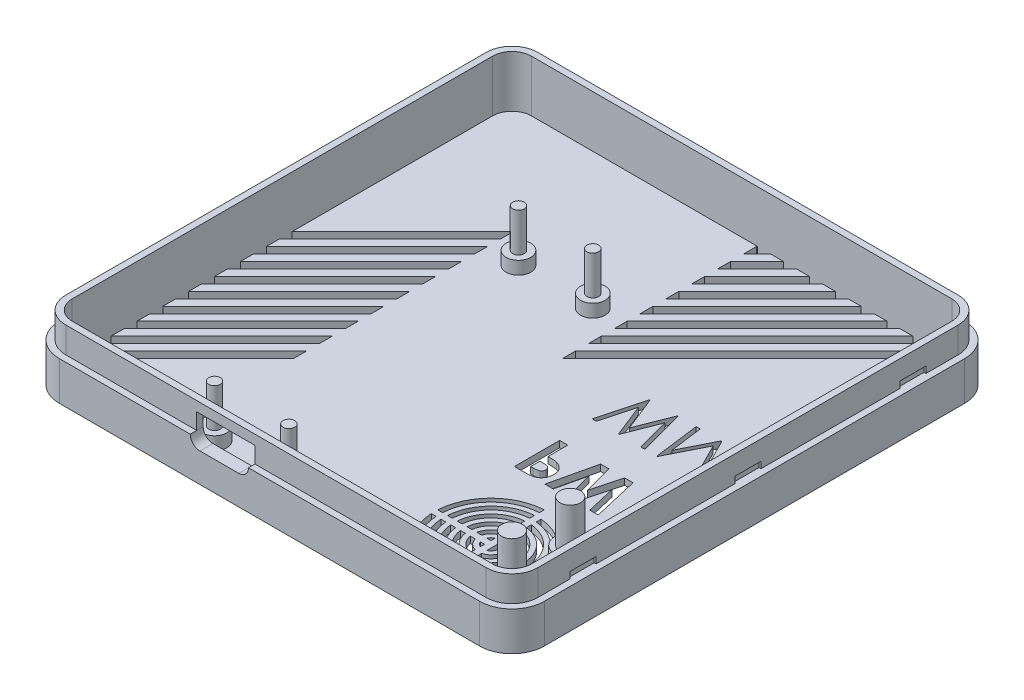
SolidWorks part; units mm, degrees
material "ABS"
ref_plane "Płaszczyzna przednia" through (0, 0, 0) normal (0, 0, 1) x (1, 0, 0)
ref_plane "Płaszczyzna górna" through (0, 0, 0) normal (0, 1, 0) x (1, 0, 0)
ref_plane "Płaszczyzna prawa" through (0, 0, 0) normal (1, 0, 0) x (0, 0, -1)
sketch "Szkic1" plane through (0, 0, 0) normal (0, 1, 0) x (1, 0, 0)
  line L0 (0, 0) -> (0, 75)
  line L1 (0, 75) -> (75, 75)
  line L2 (75, 75) -> (75, 0)
  line L3 (75, 0) -> (0, 0)
  dimension "D1" = 75
  dimension "D2" = 75
extrude "Dodanie-wyciągnięcie1" add sketch "Szkic1" along normal blind 10
fillet "Zaokrąglenie1" radius 5 4 edges at (0, 5, 0) (0, 5, -75) (75, 5, -75) (75, 5, 0)
sketch "Szkic4" plane through (0, 10, 0) normal (0, 1, 0) x (1, 0, 0)
  line L8 (2, 70) -> (2, 5)
  line L9 (5, 2) -> (70, 2)
  line L10 (73, 5) -> (73, 70)
  line L11 (70, 73) -> (5, 73)
  line L12 (2, 70) -> (2, 5)
  line L13 (5, 2) -> (70, 2)
  line L14 (73, 5) -> (73, 70)
  line L15 (70, 73) -> (5, 73)
  arc A8 (2, 5) -> (5, 2) centre (5, 5) ccw
  arc A9 (70, 2) -> (73, 5) centre (70, 5) ccw
  arc A10 (73, 70) -> (70, 73) centre (70, 70) ccw
  arc A11 (5, 73) -> (2, 70) centre (5, 70) ccw
  arc A12 (2, 5) -> (5, 2) centre (5, 5) ccw
  arc A13 (70, 2) -> (73, 5) centre (70, 5) ccw
  arc A14 (73, 70) -> (70, 73) centre (70, 70) ccw
  arc A15 (5, 73) -> (2, 70) centre (5, 70) ccw
  dimension "D1" = 2
extrude "Wytnij-wyciągnięcie1" cut sketch "Szkic4" against normal blind 8
sketch "Szkic6" plane through (0, 10, 0) normal (0, 1, 0) x (1, 0, 0)
  line L0 (70, 75) -> (5, 75)
  line L1 (0, 70) -> (0, 5)
  line L2 (5, 0) -> (70, 0)
  line L3 (75, 5) -> (75, 70)
  line L8 (1, 70) -> (1, 5)
  line L9 (5, 1) -> (70, 1)
  line L10 (74, 5) -> (74, 70)
  line L11 (70, 74) -> (5, 74)
  line L12 (1, 70) -> (1, 5)
  line L13 (5, 1) -> (70, 1)
  line L14 (74, 5) -> (74, 70)
  line L15 (70, 74) -> (5, 74)
  arc A0 (5, 75) -> (0, 70) centre (5, 70) ccw
  arc A1 (0, 5) -> (5, 0) centre (5, 5) ccw
  arc A2 (70, 0) -> (75, 5) centre (70, 5) ccw
  arc A3 (75, 70) -> (70, 75) centre (70, 70) ccw
  arc A8 (1, 5) -> (5, 1) centre (5, 5) ccw
  arc A9 (70, 1) -> (74, 5) centre (70, 5) ccw
  arc A10 (74, 70) -> (70, 74) centre (70, 70) ccw
  arc A11 (5, 74) -> (1, 70) centre (5, 70) ccw
  arc A12 (1, 5) -> (5, 1) centre (5, 5) ccw
  arc A13 (70, 1) -> (74, 5) centre (70, 5) ccw
  arc A14 (74, 70) -> (70, 74) centre (70, 70) ccw
  arc A15 (5, 74) -> (1, 70) centre (5, 70) ccw
  dimension "D1" = 1
  dimension "D3" = 1
extrude "Wytnij-wyciągnięcie2" cut sketch "Szkic6" against normal blind 4
sketch "Szkic7" plane through (0, 2, 0) normal (0, 1, 0) x (1, 0, 0)
  line L0 (2, 70) -> (2, 5) construction
  line L1 (5, 2) -> (70, 2) construction
  line L2 (5, 0) -> (70, 0) construction
  circle A0 centre (24, 52) radius 0.9
  circle A1 centre (35.5, 52) radius 0.9005
  circle A2 centre (24, 5) radius 0.9
  circle A3 centre (35.5, 5) radius 0.9
  circle A4 centre (24, 52) radius 1.9
  circle A5 centre (35.5, 52) radius 1.9005
  circle A6 centre (35.5, 5) radius 1.9
  circle A7 centre (24, 5) radius 1.9
  dimension "D1" = 22
  dimension "D3" = 1.8
  dimension "D5" = 1.801
  dimension "D7" = 1.8
  dimension "D10" = 11.5
  dimension "D11" = 1.8
  dimension "D2" = 3
  dimension "D4" = 11.5
  dimension "D6" = 5
  dimension "D8" = 47
  dimension "D12" = 47
  dimension "D14" = 22
  dimension "D13" = 1
extrude "Dodanie-wyciągnięcie2" add sketch "Szkic7" along normal blind 2
sketch "Szkic9" plane through (0, 2, 0) normal (0, 1, 0) x (1, 0, 0)
  line L4 (2, 70) -> (2, 5)
  line L5 (5, 2) -> (70, 2)
  line L6 (73, 5) -> (73, 70)
  line L7 (70, 73) -> (5, 73)
  line L8 (2, 70) -> (2, 5)
  line L9 (5, 2) -> (70, 2)
  line L10 (73, 5) -> (73, 70)
  line L11 (70, 73) -> (5, 73)
  circle A0 centre (35.5, 52) radius 0.9005 construction
  circle A1 centre (35.5, 52) radius 0.9005
  circle A2 centre (35.5, 5) radius 0.9 construction
  circle A3 centre (24, 5) radius 0.9 construction
  arc A4 (5, 73) -> (2, 70) centre (5, 70) ccw
  arc A5 (2, 5) -> (5, 2) centre (5, 5) ccw
  arc A6 (70, 2) -> (73, 5) centre (70, 5) ccw
  arc A7 (73, 70) -> (70, 73) centre (70, 70) ccw
  arc A8 (5, 73) -> (2, 70) centre (5, 70) ccw
  arc A9 (2, 5) -> (5, 2) centre (5, 5) ccw
  arc A10 (70, 2) -> (73, 5) centre (70, 5) ccw
  arc A11 (73, 70) -> (70, 73) centre (70, 70) ccw
  circle A12 centre (24, 52) radius 0.9 construction
  circle A13 centre (35.5, 5) radius 0.9
  circle A14 centre (24, 5) radius 0.9
  circle A15 centre (24, 52) radius 0.9
  dimension "D1" = 0
extrude "Dodanie-wyciągnięcie3" add sketch "Szkic9" along normal blind 8 contours A15 | A1 | A14 | A13
sketch "Szkic10" plane through (0, 2, 0) normal (0, 1, 0) x (1, 0, 0)
  line L0 (73, 5) -> (73, 70) construction
  line L1 (5, 2) -> (70, 2) construction
  circle A0 centre (67, 17) radius 1.6
  circle A1 centre (67, 8) radius 1.6
  dimension "D1" = 3.2
  dimension "D2" = 3.2
  dimension "D4" = 6
  dimension "D3" = 9
  dimension "D5" = 6
  dimension "D6" = 15
extrude "Dodanie-wyciągnięcie4" add sketch "Szkic10" along normal blind 8
sketch "Szkic11" plane through (0, 2, 0) normal (0, 1, 0) x (1, 0, 0)
  line L4 (2, 70) -> (2, 5)
  line L5 (5, 2) -> (70, 2)
  line L6 (73, 5) -> (73, 70)
  line L7 (70, 73) -> (5, 73)
  line L8 (2, 70) -> (2, 5)
  line L9 (5, 2) -> (70, 2)
  line L10 (73, 5) -> (73, 70)
  line L11 (70, 73) -> (5, 73)
  circle A0 centre (67, 8) radius 1.6 construction
  circle A1 centre (67, 17) radius 1.6 construction
  circle A2 centre (67, 8) radius 1.6
  circle A3 centre (67, 17) radius 1.6
  arc A4 (5, 73) -> (2, 70) centre (5, 70) ccw
  arc A5 (2, 5) -> (5, 2) centre (5, 5) ccw
  arc A6 (70, 2) -> (73, 5) centre (70, 5) ccw
  arc A7 (73, 70) -> (70, 73) centre (70, 70) ccw
  arc A8 (5, 73) -> (2, 70) centre (5, 70) ccw
  arc A9 (2, 5) -> (5, 2) centre (5, 5) ccw
  arc A10 (70, 2) -> (73, 5) centre (70, 5) ccw
  arc A11 (73, 70) -> (70, 73) centre (70, 70) ccw
  circle A12 centre (67, 17) radius 2.35
  circle A13 centre (67, 8) radius 2.35
  circle M9 centre (67, 8) radius 1.6
  circle M10 centre (67, 17) radius 1.6
  dimension "D1" = 0
  dimension "D2" = 0.75
extrude "Dodanie-wyciągnięcie5" add sketch "Szkic11" along normal blind 1.5 contours A12 M10 | A13 M9
sketch "Szkic14" plane through (0, 2, 0) normal (0, 1, 0) x (1, 0, 0)
  line L0 (52, 73) -> (2, 23)
  line L1 (70, 73) -> (5, 73) construction
  line L2 (2, 70) -> (2, 5) construction
  line L3 (54, 73) -> (2, 21)
  line L4 (56, 73) -> (2, 19)
  line L5 (58, 73) -> (2, 17)
  line L6 (60, 73) -> (2, 15)
  line L7 (2, 23) -> (2, 21)
  line L8 (62, 73) -> (2, 13)
  line L9 (2, 25) -> (50, 73)
  line L10 (46, 73) -> (2, 29)
  line L12 (2, 27) -> (48, 73)
  line L13 (2, 11) -> (64, 73)
  line L14 (2, 9) -> (66, 73)
  line L15 (2, 7) -> (68, 73)
  line L16 (2, 5) -> (70, 73)
  line L18 (2, 19) -> (2, 17)
  line L19 (2, 15) -> (2, 13)
  line L20 (2, 11) -> (2, 9)
  line L21 (2, 7) -> (2, 5)
  line L22 (48, 73) -> (50, 73)
  line L23 (52, 73) -> (54, 73)
  line L24 (56, 73) -> (58, 73)
  line L25 (60, 73) -> (62, 73)
  line L26 (64, 73) -> (66, 73)
  line L27 (68, 73) -> (70, 73)
  line L30 (2, 70) -> (2, 5) construction
  line L31 (2, 27) -> (2, 25)
  line L32 (2, 31) -> (44, 73)
  line L33 (44, 73) -> (46, 73)
  line L34 (2, 31) -> (2, 29)
  line L35 (2, 33) -> (42, 73)
  line L36 (38, 73) -> (2, 37)
  line L37 (40, 73) -> (2, 35)
  line L38 (2, 39) -> (36, 73)
  line L41 (39.899, 22) -> (19.1028, 22)
  line L42 (39.899, 73) -> (39.899, 22)
  line L46 (19.1028, 73) -> (39.899, 73)
  line L49 (19.1028, 73) -> (19.1028, 22)
  arc A2 (-2.3435, 2.6565) -> (-0.8972, 2.1028) centre (-1, 4) ccw
  arc A3 (0.8972, 3.8972) -> (0.3435, 5.3435) centre (-1, 4) ccw
  point P34 (19.1028, 52.9005)
  line M13 (2, 70) -> (2, 5)
  line M19 (70, 73) -> (5, 73)
  dimension "D1" = 2
  dimension "D2" = 2
  dimension "D3" = 2
  dimension "D4" = 2
  dimension "D5" = 2
  dimension "D6" = 2
  dimension "D7" = 2
  dimension "D8" = 2
  dimension "D9" = 2
  dimension "D10" = 2
  dimension "D11" = 2
  dimension "D12" = 2
  dimension "D13" = 2
  dimension "D14" = 2
  dimension "D15" = 2
  dimension "D16" = 2
  dimension "D17" = 2
  dimension "D18" = 2
  dimension "D19" = 51
  dimension "D20" = 20.7962
  dimension "D21" = 17.1028
  dimension "D22" = 0
sketch "Szkic15" plane through (0, 2, 0) normal (0, 1, 0) x (1, 0, 0)
  line L1 (58.75, 23) -> (59.75, 23)
  line L2 (58.75, 23) -> (58.75, 13)
  line L3 (58.75, 2) -> (59.75, 2)
  line L4 (59.75, 23) -> (59.75, 13)
  line L5 (48.75, 13) -> (58.75, 13)
  line L6 (48.75, 13) -> (48.75, 12)
  line L7 (48.75, 12) -> (58.75, 12)
  line L8 (69.75, 13) -> (69.75, 12)
  line L9 (67.9857, 12) -> (69.75, 12)
  line L10 (59.75, 12) -> (59.75, 2)
  line L11 (58.75, 12) -> (58.75, 2)
  line L12 (59.75, 13) -> (59.25, 12.5)
  line L13 (58.75, 13) -> (59.75, 12) construction
  line L14 (59.75, 13) -> (58.75, 12) construction
  line L15 (73, 5) -> (73, 70) construction
  line L16 (59.25, 12.5) -> (62, 12.5) construction
  line L17 (5, 2) -> (70, 2) construction
  line L18 (64.9939, 12.2356) -> (67.9854, 11.9955)
  line L19 (59.75, 12) -> (84.751, 13)
  line L20 (59.9237, 13.5529) -> (61.1553, 13.108)
  line L21 (67.9857, 13) -> (69.75, 13)
  line L22 (64.9387, 13.3374) -> (67.8134, 14.2973)
  line L23 (64.9939, 12.7644) -> (67.9854, 13.0045)
  line L24 (68, 12.5) -> (69.75, 12.5) construction
  line L25 (64.9492, 11.7375) -> (67.8134, 10.7027)
  line L26 (63.4934, 12.2634) -> (64.2248, 11.9991)
  line L27 (61.9826, 12.8092) -> (62.7499, 12.532)
  line L28 (59.75, 13.6456) -> (59.75, 11.3544)
  arc A0 (59.75, 18.2282) -> (64.9992, 12.5935) centre (59.25, 12.5) cw
  circle A1 centre (67, 17) radius 1.6 construction
  arc A2 (58.75, 13.6456) -> (58.1044, 13) centre (59.25, 12.5) ccw
  arc A3 (58.75, 14.4365) -> (57.3135, 13) centre (59.25, 12.5) ccw
  arc A4 (58.75, 15.2042) -> (56.5458, 13) centre (59.25, 12.5) ccw
  arc A5 (58.75, 15.9641) -> (55.7859, 13) centre (59.25, 12.5) ccw
  arc A6 (58.75, 16.7205) -> (55.0295, 13) centre (59.25, 12.5) ccw
  arc A7 (58.75, 17.4749) -> (54.2751, 13) centre (59.25, 12.5) ccw
  arc A8 (58.75, 18.2282) -> (53.5218, 13) centre (59.25, 12.5) ccw
  arc A9 (58.75, 18.9807) -> (52.7693, 13) centre (59.25, 12.5) ccw
  arc A10 (58.75, 19.7327) -> (52.0173, 13) centre (59.25, 12.5) ccw
  arc A11 (58.75, 20.4844) -> (51.2656, 13) centre (59.25, 12.5) ccw
  arc A12 (58.75, 21.2357) -> (50.5143, 13) centre (59.25, 12.5) ccw
  arc A13 (60.4998, 12.5221) -> (59.75, 13.6456) centre (59.25, 12.5) ccw
  arc A14 (61.2497, 12.5371) -> (59.75, 14.4365) centre (59.25, 12.5) ccw
  arc A15 (61.9996, 12.5496) -> (59.75, 15.2042) centre (59.25, 12.5) ccw
  arc A16 (62.7495, 12.5615) -> (59.75, 15.9641) centre (59.25, 12.5) ccw
  arc A17 (63.4994, 12.5727) -> (59.75, 16.7205) centre (59.25, 12.5) ccw
  arc A18 (59.75, 17.4749) -> (64.2493, 12.5834) centre (59.25, 12.5) cw
  arc A19 (59.75, 21.2357) -> (67.8134, 14.2973) centre (59.25, 12.5) cw
  arc A20 (59.75, 20.4844) -> (67.1021, 14.031) centre (59.25, 12.5) cw
  arc A21 (59.75, 19.7327) -> (66.3858, 13.7815) centre (59.25, 12.5) cw
  arc A22 (59.75, 18.9807) -> (65.6646, 13.5499) centre (59.25, 12.5) cw
  arc A23 (66.4902, 12.1223) -> (66.4991, 12.3876) centre (59.25, 12.5) ccw
  arc A24 (59.75, 3.7643) -> (67.8134, 10.7027) centre (59.25, 12.5) ccw
  arc A25 (59.75, 4.5156) -> (67.1004, 10.9603) centre (59.25, 12.5) ccw
  arc A26 (59.75, 5.2673) -> (66.3858, 11.2185) centre (59.25, 12.5) ccw
  arc A27 (59.75, 6.0193) -> (65.6691, 11.4774) centre (59.25, 12.5) ccw
  arc A28 (59.75, 6.7718) -> (64.9992, 12.4065) centre (59.25, 12.5) ccw
  arc A29 (59.75, 7.5251) -> (64.2493, 12.4166) centre (59.25, 12.5) ccw
  arc A30 (59.75, 8.2795) -> (63.4994, 12.4273) centre (59.25, 12.5) ccw
  arc A31 (59.75, 9.0359) -> (62.7495, 12.4385) centre (59.25, 12.5) ccw
  arc A32 (59.75, 9.7958) -> (61.9996, 12.4504) centre (59.25, 12.5) ccw
  arc A33 (59.75, 10.5635) -> (61.2497, 12.4629) centre (59.25, 12.5) ccw
  arc A34 (59.75, 11.3544) -> (60.4998, 12.4761) centre (59.25, 12.5) ccw
  arc A35 (58.1044, 12) -> (58.75, 11.3544) centre (59.25, 12.5) ccw
  arc A36 (57.3135, 12) -> (58.75, 10.5635) centre (59.25, 12.5) ccw
  arc A37 (56.5458, 12) -> (58.75, 9.7958) centre (59.25, 12.5) ccw
  arc A38 (55.7859, 12) -> (58.75, 9.0359) centre (59.25, 12.5) ccw
  arc A39 (55.0295, 12) -> (58.75, 8.2795) centre (59.25, 12.5) ccw
  arc A40 (54.2751, 12) -> (58.75, 7.5251) centre (59.25, 12.5) ccw
  arc A41 (53.5218, 12) -> (58.75, 6.7718) centre (59.25, 12.5) ccw
  arc A42 (52.7693, 12) -> (58.75, 6.0193) centre (59.25, 12.5) ccw
  arc A43 (52.0173, 12) -> (58.75, 5.2673) centre (59.25, 12.5) ccw
  arc A44 (51.2656, 12) -> (58.75, 4.5156) centre (59.25, 12.5) ccw
  arc A45 (50.5143, 12) -> (58.75, 3.7643) centre (59.25, 12.5) ccw
  arc A46 (67.2379, 12.0605) -> (67.2491, 12.3787) centre (59.25, 12.5) ccw
  arc A47 (67.9854, 11.9955) -> (67.9857, 12) centre (59.25, 12.5) ccw
  arc A48 (65.7422, 12.1808) -> (65.7492, 12.3968) centre (59.25, 12.5) ccw
  arc A49 (67.9854, 13.0045) -> (67.9857, 13) centre (59.25, 12.5) cw
  arc A50 (67.2379, 12.9395) -> (67.2491, 12.6213) centre (59.25, 12.5) cw
  arc A51 (66.4902, 12.8777) -> (66.4991, 12.6124) centre (59.25, 12.5) cw
  arc A52 (65.7422, 12.8192) -> (65.7492, 12.6032) centre (59.25, 12.5) cw
  arc A53 (60.4998, 12.5239) -> (60.4996, 12.4699) centre (59.25, 12.5) cw
  arc A54 (61.2497, 12.5371) -> (61.2497, 12.4629) centre (59.25, 12.5) cw
  arc A55 (61.9996, 12.5496) -> (61.9996, 12.4504) centre (59.25, 12.5) cw
  arc A56 (62.7495, 12.5615) -> (62.7494, 12.4362) centre (59.25, 12.5) cw
  arc A57 (63.4994, 12.5727) -> (63.4994, 12.4273) centre (59.25, 12.5) cw
  arc A58 (64.2493, 12.5834) -> (64.2493, 12.4166) centre (59.25, 12.5) cw
  arc A59 (64.9992, 12.5935) -> (64.9992, 12.4065) centre (59.25, 12.5) cw
  arc A60 (65.7492, 12.6032) -> (65.7492, 12.3968) centre (59.25, 12.5) cw
  arc A61 (66.4991, 12.6124) -> (66.4991, 12.3876) centre (59.25, 12.5) cw
  arc A62 (67.2491, 12.6213) -> (67.2491, 12.3787) centre (59.25, 12.5) cw
  arc A63 (67.9857, 13) -> (67.9857, 12) centre (59.25, 12.5) cw
  dimension "D9" = 2.5
  dimension "D10" = 4
  dimension "D11" = 5.5
  dimension "D12" = 7
  dimension "D13" = 8.5
  dimension "D14" = 10
  dimension "D15" = 11.5
  dimension "D16" = 13
  dimension "D17" = 14.5
  dimension "D18" = 16
  dimension "D19" = 17.5
  dimension "D1" = 1
  dimension "D2" = 1
  dimension "D5" = 10
  dimension "D6" = 10
  dimension "D7" = 10
  dimension "D8" = 7.25
  dimension "D20" = 13.75
  dimension "D21" = 10.5
sketch "Szkic16" plane through (0, 0, 0) normal (0, -1, 0) x (1, 0, 0)
  line L8 (70, -1) -> (5, -1)
  line L9 (1, -5) -> (1, -70)
  line L10 (5, -74) -> (70, -74)
  line L11 (74, -70) -> (74, -5)
  line L12 (70, -1) -> (5, -1)
  line L13 (1, -5) -> (1, -70)
  line L14 (5, -74) -> (70, -74)
  line L15 (74, -70) -> (74, -5)
  arc A8 (5, -1) -> (1, -5) centre (5, -5) ccw
  arc A9 (1, -70) -> (5, -74) centre (5, -70) ccw
  arc A10 (70, -74) -> (74, -70) centre (70, -70) ccw
  arc A11 (74, -5) -> (70, -1) centre (70, -5) ccw
  arc A12 (5, -1) -> (1, -5) centre (5, -5) ccw
  arc A13 (1, -70) -> (5, -74) centre (5, -70) ccw
  arc A14 (70, -74) -> (74, -70) centre (70, -70) ccw
  arc A15 (74, -5) -> (70, -1) centre (70, -5) ccw
  dimension "D1" = 1
extrude "Wytnij-wyciągnięcie13" cut sketch "Szkic15" against normal blind 10
extrude "Wytnij-wyciągnięcie6" cut sketch "Szkic16" against normal blind 1
sketch "Szkic18" plane through (0, 1, 0) normal (0, -1, 0) x (1, 0, 0)
  text T1 "<b>PW</b>\r\nWMT" font "Century Gothic" height 7
  point P0 (49.8345, -31.7272)
extrude "Wytnij-wyciągnięcie9" cut sketch "Szkic18" against normal through all both and the other way through all
sketch "Szkic19" plane through (0, 0, -2) normal (0, 0, -1) x (-1, 0, 0)
  line L0 (-29.75, 2) -> (-29.75, 10) construction
  line L1 (-5, 2) -> (-70, 2) construction
  line L2 (-2, 2) -> (-2, 10) construction
  line L3 (-5, 6) -> (-5, 10) construction
  line L8 (-32.75, 4.5) -> (-26.75, 4.5)
  line L9 (-34.25, 6) -> (-34.25, 8.5)
  line L10 (-34.25, 8.5) -> (-25.25, 8.5)
  line L11 (-25.25, 6) -> (-25.25, 8.5)
  arc A1 (-25.25, 6) -> (-26.75, 4.5) centre (-26.75, 6) cw
  arc A2 (-32.75, 4.5) -> (-34.25, 6) centre (-32.75, 6) cw
  dimension "D2" = 1.5
  dimension "D1" = 27.75
  dimension "D4" = 4.5
  dimension "D5" = 9
  dimension "D6" = 2.5
  dimension "D7" = 4
sketch "Szkic20" plane through (1, 0, 0) normal (-1, 0, 0) x (0, 0, 1)
  line L0 (-70, 6) -> (-5, 6) construction
  line L1 (-65, 6) -> (-61, 6)
  line L2 (-65, 6) -> (-65, 7)
  line L3 (-65, 7) -> (-61, 7)
  line L4 (-61, 6) -> (-61, 7)
  line L5 (-14, 7) -> (-10, 7)
  line L6 (-14, 6) -> (-14, 7)
  line L7 (-14, 6) -> (-10, 6)
  line L8 (-10, 6) -> (-10, 7)
  line L9 (0, 6) -> (0, 0) construction
  line L10 (-39.5, 7) -> (-35.5, 7)
  line L11 (-35.5, 6) -> (-35.5, 7)
  line L12 (-39.5, 6) -> (-35.5, 6)
  line L13 (-39.5, 6) -> (-39.5, 7)
  point P14 (-63, 6)
  point P18 (-37.5, 6)
  dimension "D1" = 1
  dimension "D2" = 4
  dimension "D3" = 10
  dimension "D5" = 10
  dimension "D7" = 25.5
  dimension "D4" = 2
  dimension "D6" = 2
extrude "Wytnij-wyciągnięcie11" cut sketch "Szkic20" against normal blind 0.3
sketch "Szkic21" plane through (74, 0, 0) normal (1, 0, 0) x (0, 0, -1)
  line L0 (5, 6) -> (70, 6) construction
  line L1 (10, 6) -> (14, 6)
  line L2 (10, 6) -> (10, 7)
  line L3 (10, 7) -> (14, 7)
  line L4 (14, 6) -> (14, 7)
  line L5 (0, 0) -> (0, 6) construction
  line L6 (61, 7) -> (65, 7)
  line L7 (61, 6) -> (61, 7)
  line L8 (61, 6) -> (65, 6)
  line L9 (65, 6) -> (65, 7)
  line L10 (75, 6) -> (75, 0) construction
  line L11 (35.5, 7) -> (39.5, 7)
  line L12 (35.5, 6) -> (35.5, 7)
  line L13 (35.5, 6) -> (39.5, 6)
  line L14 (39.5, 6) -> (39.5, 7)
  point P15 (12, 6)
  point P19 (37.5, 6)
  dimension "D1" = 4
  dimension "D2" = 1
  dimension "D3" = 10
  dimension "D5" = 10
  dimension "D7" = 25.5
  dimension "D4" = 2
  dimension "D6" = 2
extrude "Wytnij-wyciągnięcie12" cut sketch "Szkic21" against normal blind 0.3
ref_plane "Płaszczyzna1" through (0, 0, -25) normal (0, 0, -1) x (-1, 0, 0)
extrude "Wytnij-wyciągnięcie14" cut sketch "Szkic14" against normal blind 10 contours L49 L15 L16 M13 | L49 L13 L14 M13 | L49 L6 L8 M13 | L49 L4 L5 M13 | L49 L0 L3 M13 | L49 L12 L9 M13 | L49 L32 L10 M13 | L49 L37 L35 M13 | L49 L38 L36 M13 | L37 L42 L35 M19 | L32 L42 L10 M19 | L12 L42 L9 M19 | L0 L42 L3 M19 | L4 L42 L5 M19 | L6 L42 L8 M19 | L13 L42 L14 M19 | L15 L42 L16 M19
extrude "Wytnij-wyciągnięcie15" cut sketch "Szkic19" against normal blind 10
